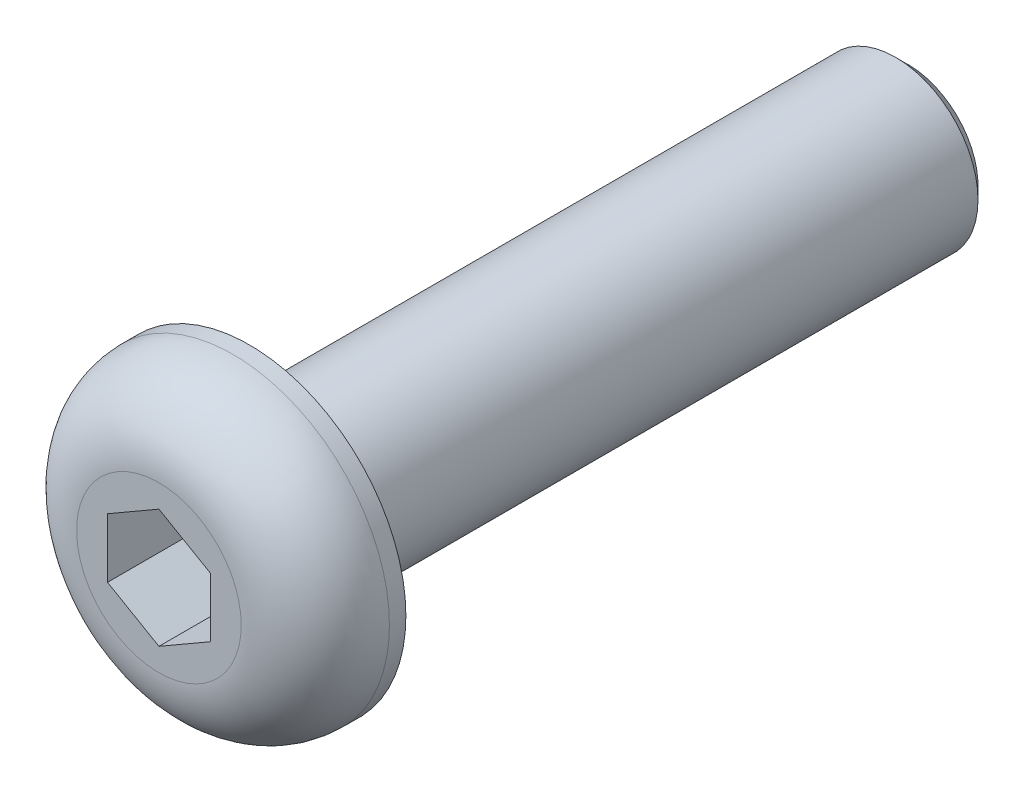
SolidWorks part; units mm, degrees
ref_plane "Front Plane" through (0, 0, 0) normal (0, 0, 1) x (1, 0, 0)
ref_plane "Top Plane" through (0, 0, 0) normal (0, 1, 0) x (1, 0, 0)
ref_plane "Right Plane" through (0, 0, 0) normal (1, 0, 0) x (0, 0, -1)
sketch "Sketch1" plane through (0, 0, 0) normal (0, 0, 1) x (1, 0, 0)
  circle A0 centre (0, 0) radius 3.8
  dimension "D1" = 7.6
extrude "Boss-Extrude1" add sketch "Sketch1" along normal blind 2.2
sketch "Sketch2" plane through (0, 0, 0) normal (0, 0, -1) x (-1, 0, 0)
  circle A0 centre (0, 0) radius 2
  dimension "D1" = 4
extrude "Boss-Extrude2" add sketch "Sketch2" along normal blind 16
chamfer "Chamfer1" distance 0.3 angle 45 1 edges at (-2, 0, -16)
sketch "Sketch3" plane through (0, 0, 2.2) normal (0, 0, 1) x (1, 0, 0)
  line L1 (0, 1.4434) -> (-1.25, 0.7217)
  line L2 (-1.25, 0.7217) -> (-1.25, -0.7217)
  line L3 (-1.25, -0.7217) -> (0, -1.4434)
  line L4 (0, -1.4434) -> (1.25, -0.7217)
  line L5 (1.25, -0.7217) -> (1.25, 0.7217)
  line L6 (1.25, 0.7217) -> (0, 1.4434)
  circle A0 centre (0, 0) radius 1.25 construction
  dimension "D1" = 2.5
extrude "Cut-Extrude1" cut sketch "Sketch3" against normal blind 2
fillet "Fillet1" radius 1.8 1 edges at (3.8, 0, 2.2)
